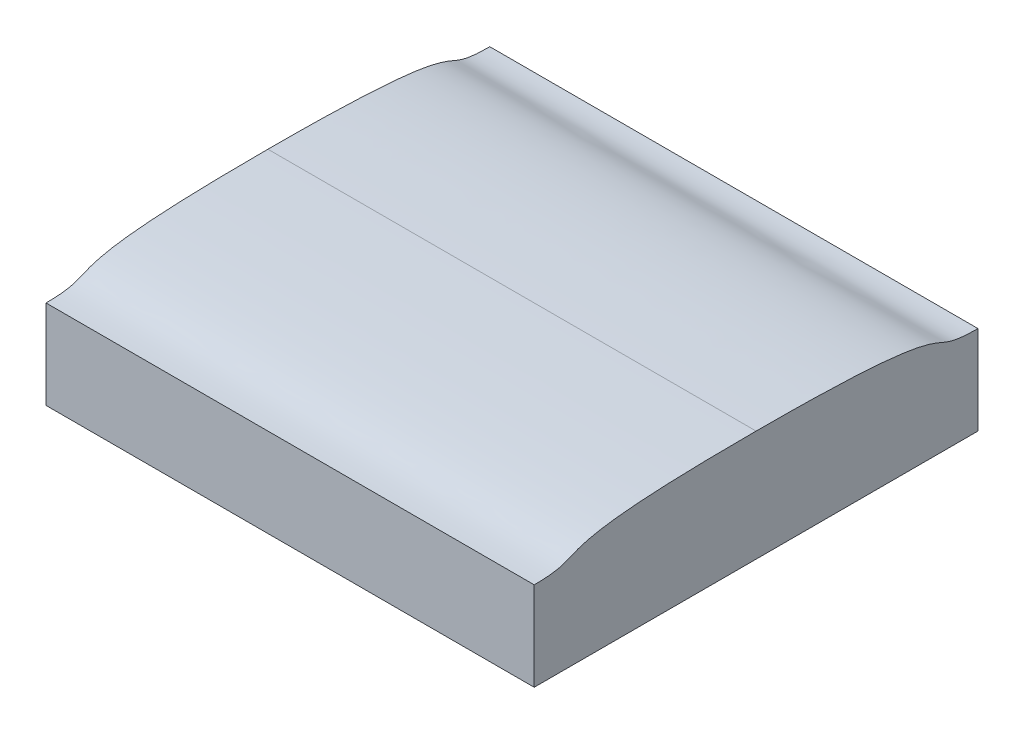
SolidWorks part; units mm, degrees
ref_plane "Front Plane" through (0, 0, 0) normal (0, 0, 1) x (1, 0, 0)
ref_plane "Top Plane" through (0, 0, 0) normal (0, 1, 0) x (1, 0, 0)
ref_plane "Right Plane" through (0, 0, 0) normal (1, 0, 0) x (0, 0, -1)
sketch "Sketch1" plane through (0, 0, 0) normal (1, 0, 0) x (0, 0, -1)
  line L0 (0, 0) -> (0, 10.6913) construction
  line L1 (10, -0.2307) -> (10, 3.7693)
  line L2 (-4.8433, -0.2307) -> (4.8433, -0.2307) construction
  line L3 (-3.6834, 4.7693) -> (3.6834, 4.7693) construction
  line L4 (7.153, 3.7693) -> (13.5837, 3.7693) construction
  line L5 (-10, -0.2307) -> (-10, 3.7693)
  spline S0 degree 3 poles (10, -0.2307) (5.3899, -0.2307) (8.6691, -0.2307) (0, -0.2307) knots 0 0 0 0 1 1 1 1
  spline S1 degree 3 poles (10, 3.7693) (7.1601, 3.7693) (10.1681, 4.7693) (0, 4.7693) knots 0 0 0 0 1 1 1 1
  spline S2 degree 3 poles (-10, -0.2307) (-5.3899, -0.2307) (-8.6691, -0.2307) (0, -0.2307) knots 0 0 0 0 1 1 1 1
  spline S3 degree 3 poles (-10, 3.7693) (-7.1601, 3.7693) (-10.1681, 4.7693) (0, 4.7693) knots 0 0 0 0 1 1 1 1
  point P13 (10, 1.7693)
  point P16 (-10, 1.7693)
  dimension "D1" = 4
  dimension "D2" = 0
  dimension "D3" = 0
  dimension "D4" = 20
  dimension "D5" = 5
extrude "Boss-Extrude1" add sketch "Sketch1" along normal blind 22
